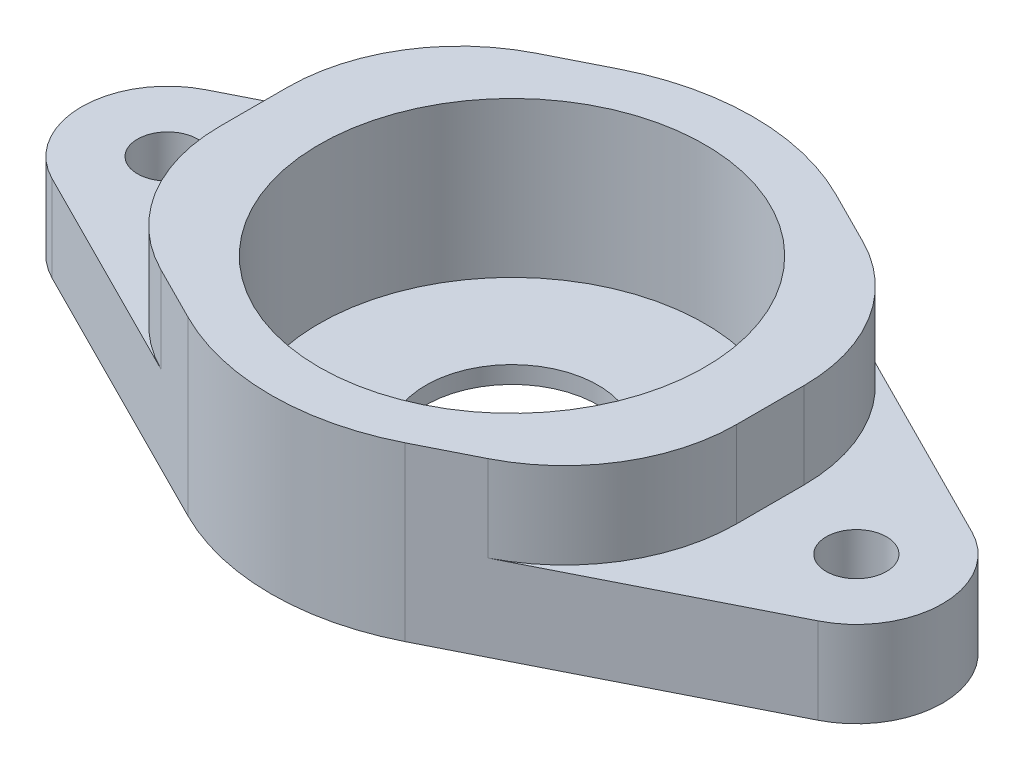
SolidWorks part; units mm, degrees
ref_plane "Front Plane" through (0, 0, 0) normal (0, 0, 1) x (1, 0, 0)
ref_plane "Top Plane" through (0, 0, 0) normal (0, 1, 0) x (1, 0, 0)
ref_plane "Right Plane" through (0, 0, 0) normal (1, 0, 0) x (0, 0, -1)
sketch "Sketch2" plane through (0, 0, 0) normal (0, 1, 0) x (1, 0, 0)
  line L0 (-22.25, 4.4651) -> (-6.3, 12.5024)
  line L1 (6.3, 12.5024) -> (22.25, 4.4651)
  line L2 (-22.25, -4.4651) -> (-6.3, -12.5024)
  line L3 (6.3, -12.5024) -> (22.25, -4.4651)
  arc A0 (6.3, 12.5024) -> (-6.3, 12.5024) centre (0, 0) ccw
  arc A1 (-22.25, 4.4651) -> (-22.25, -4.4651) centre (-20, 0) ccw
  arc A2 (22.25, -4.4651) -> (22.25, 4.4651) centre (20, 0) ccw
  circle A4 centre (-20, 0) radius 1.75
  circle A5 centre (20, 0) radius 1.75
  arc A6 (-6.3, -12.5024) -> (6.3, -12.5024) centre (0, 0) ccw
  dimension "D1" = 28
  dimension "D2" = 10
  dimension "D3" = 10
  dimension "D4" = 3.5
  dimension "D5" = 3.5
  dimension "D6" = 20
  dimension "D7" = 20
extrude "Boss-Extrude1" add sketch "Sketch2" along normal blind 10
sketch "Sketch3" plane through (0, 10, 0) normal (0, 1, 0) x (1, 0, 0)
  circle A0 centre (0, 0) radius 11.2
  dimension "D1" = 22.4
extrude "Cut-Extrude1" cut sketch "Sketch3" against normal blind 9
sketch "Sketch4" plane through (0, 0, 0) normal (0, 0, 1) x (1, 0, 0)
  line L0 (-22.25, 10) -> (-6.3, 10) construction
  line L1 (-15, 10) -> (-25, 10)
  line L2 (-15, 10) -> (-15, 5)
  line L3 (-15, 5) -> (-25, 5)
  line L4 (-25, 10) -> (-25, 5)
  line L5 (-25, 10) -> (-25, 0) construction
  line L6 (6.3, 10) -> (22.25, 10) construction
  line L7 (15, 10) -> (25, 10)
  line L8 (15, 10) -> (15, 5)
  line L9 (15, 5) -> (25, 5)
  line L10 (25, 10) -> (25, 5)
  line L11 (25, 0) -> (25, 10) construction
  line L12 (-22.25, 0) -> (-6.3, 0) construction
  line L13 (18.25, 0) -> (21.75, 0) construction
  dimension "D1" = 10
  dimension "D2" = 10
  dimension "D3" = 5
  dimension "D4" = 5
extrude "Cut-Extrude2" cut sketch "Sketch4" against normal through all both and the other way through all
fillet "Fillet1" radius 10 4 edges at (15, 7.5, 8.1184) (15, 7.5, -8.1184) (-15, 7.5, -8.1184) (-15, 7.5, 8.1184)
sketch "Sketch5" plane through (0, 1, 0) normal (0, 1, 0) x (1, 0, 0)
  circle A0 centre (0, 0) radius 5
  dimension "D1" = 10
extrude "Cut-Extrude3" cut sketch "Sketch5" against normal through all both and the other way through all
